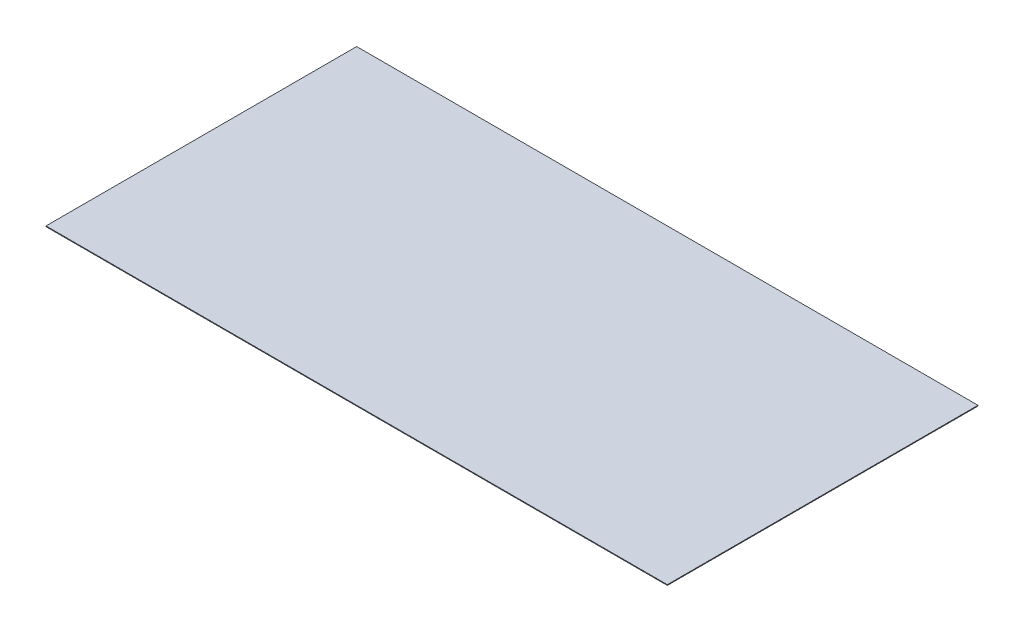
SolidWorks part; units mm, degrees
material "1023 Carbon Steel Sheet (SS)"
ref_plane "Front Plane" through (0, 0, 0) normal (0, 0, 1) x (1, 0, 0)
ref_plane "Top Plane" through (0, 0, 0) normal (0, 1, 0) x (1, 0, 0)
ref_plane "Right Plane" through (0, 0, 0) normal (1, 0, 0) x (0, 0, -1)
sketch "Sketch1" plane through (0, 0, 0) normal (0, 1, 0) x (1, 0, 0)
  line L1 (-450, 225) -> (450, 225)
  line L2 (-450, 225) -> (-450, -225)
  line L3 (-450, -225) -> (450, -225)
  line L4 (450, 225) -> (450, -225)
  line L5 (-450, 225) -> (450, -225) construction
  line L6 (-450, -225) -> (450, 225) construction
  point P0 (0, 0)
  dimension "D1" = 450
  dimension "D2" = 900
extrude "Boss-Extrude1" add sketch "Sketch1" along normal blind 1
